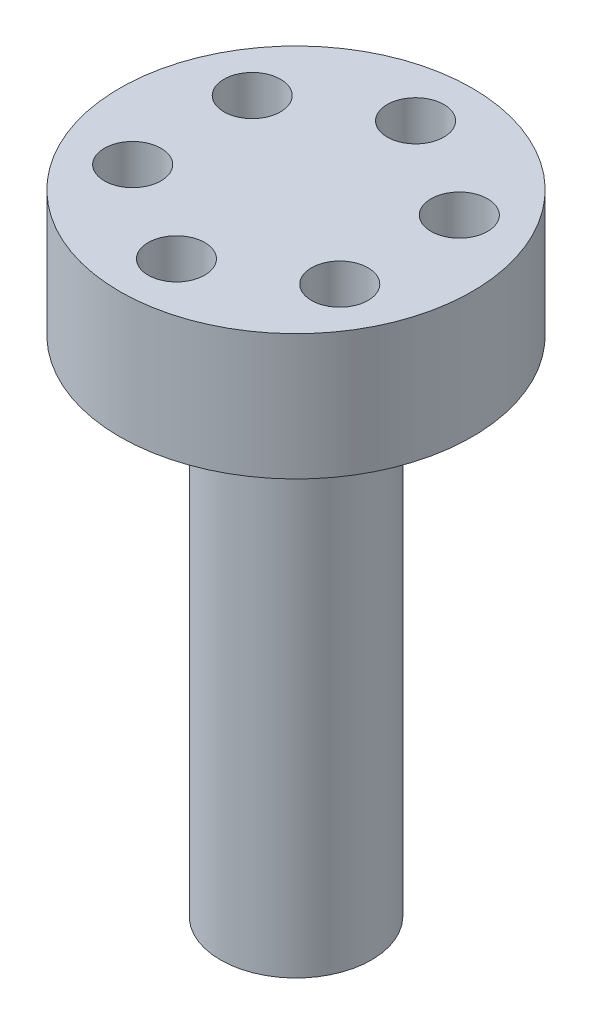
SolidWorks part; units mm, degrees
ref_plane "Front Plane" through (0, 0, 0) normal (0, 0, 1) x (1, 0, 0)
ref_plane "Top Plane" through (0, 0, 0) normal (0, 1, 0) x (1, 0, 0)
ref_plane "Right Plane" through (0, 0, 0) normal (1, 0, 0) x (0, 0, -1)
sketch "Sketch1" plane through (0, 0, 0) normal (0, 1, 0) x (1, 0, 0)
  circle A0 centre (0, 0) radius 6
  dimension "D1" = 12
extrude "Boss-Extrude1" add sketch "Sketch1" along normal mid plane 40
sketch "Sketch4" plane through (0, 20, 0) normal (0, 1, 0) x (1, 0, 0)
  circle A0 centre (0, 0) radius 14
  dimension "D1" = 28
extrude "Boss-Extrude2" add sketch "Sketch4" along normal blind 10
sketch "Sketch5" plane through (0, 30, 0) normal (0, 1, 0) x (1, 0, 0)
  line L0 (0, 0) -> (0, 9.5) construction
  circle A0 centre (0, 9.5) radius 2.25
  dimension "D1" = 4.5
  dimension "D2" = 9.5
extrude "Cut-Extrude2" cut sketch "Sketch5" against normal blind 10
pattern_circular "CirPattern1" count 6 over 360 about axis through (0, 0, 0) along (0, 1, 0) of "Cut-Extrude2"
sketch "Sketch7" plane through (0, -20, 0) normal (0, -1, 0) x (1, 0, 0)
  line L0 (0, 0) -> (0, 3) construction
  circle A0 centre (0, 3) radius 1.75
  dimension "D1" = 3.5
  dimension "D2" = 3
extrude "Cut-Extrude3" cut sketch "Sketch7" against normal blind 10
pattern_circular "CirPattern2" count 3 over 360 about axis through (0, 0, 0) along (0, 1, 0) of "Cut-Extrude3"
